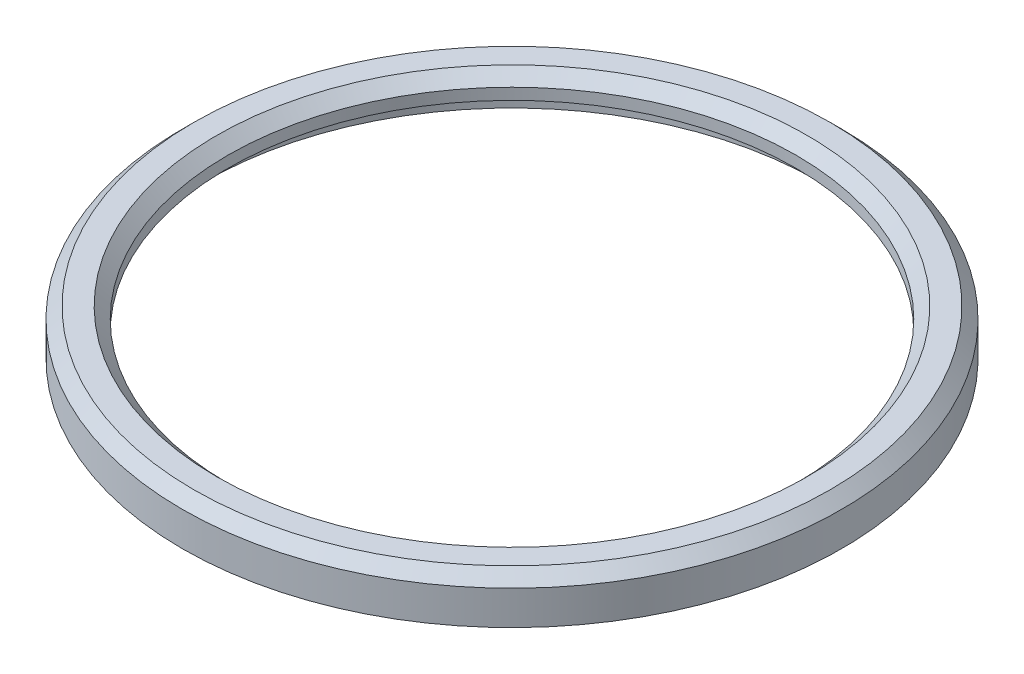
SolidWorks part; units mm, degrees
ref_plane "Front Plane" through (0, 0, 0) normal (0, 0, 1) x (1, 0, 0)
ref_plane "Top Plane" through (0, 0, 0) normal (0, 1, 0) x (1, 0, 0)
ref_plane "Right Plane" through (0, 0, 0) normal (1, 0, 0) x (0, 0, -1)
sketch "Sketch1" plane through (0, 0, 0) normal (0, 1, 0) x (1, 0, 0)
  circle A0 centre (0, 0) radius 13.5 construction
  circle A1 centre (0, 0) radius 14.5
  circle A2 centre (0, 0) radius 12.5
  dimension "D1" = 27
  dimension "D2" = 1
  dimension "D3" = 1
extrude "Boss-Extrude1" add sketch "Sketch1" along normal blind 2
sketch "Sketch2" plane through (0, 0, 0) normal (0, -1, 0) x (1, 0, 0)
  circle A2 centre (0, 0) radius 13.5
  circle A3 centre (0, 0) radius 13.5
  dimension "D1" = 1
extrude "Cut-Extrude1" cut sketch "Sketch2" against normal blind 1
chamfer "Chamfer1" distance 0.5 angle 45 2 edges at (0, 2, 14.5) (0, 2, 12.5)
